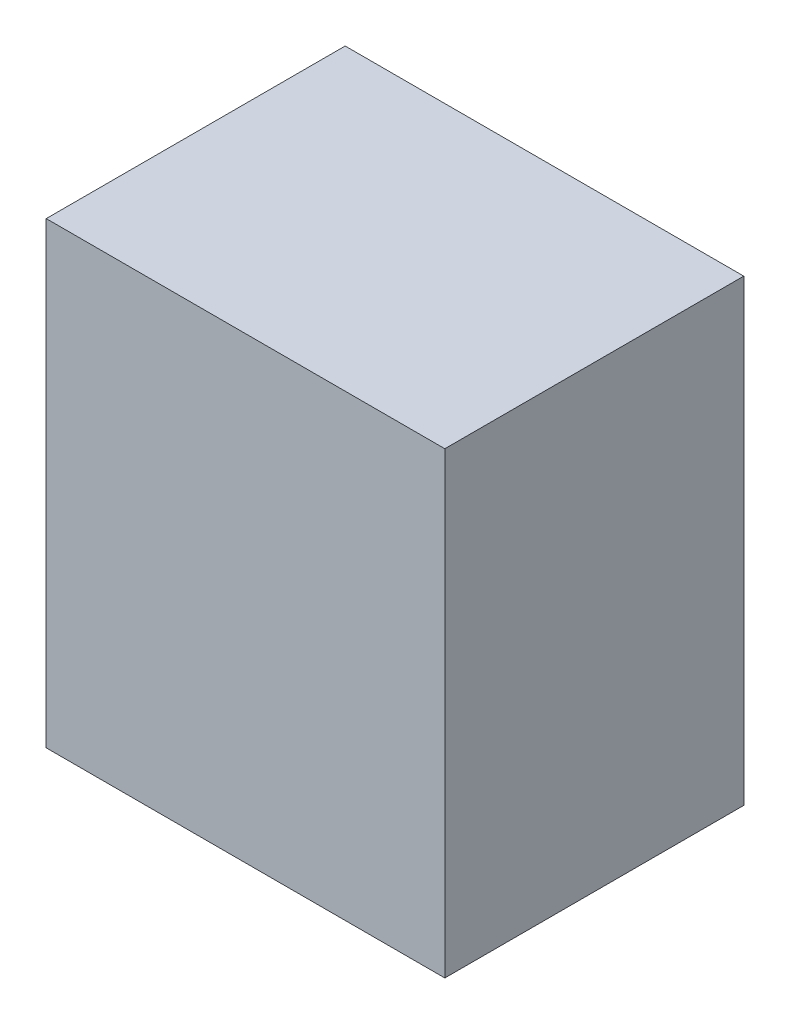
SolidWorks part; units mm, degrees
ref_plane "Front Plane" through (0, 0, 0) normal (0, 0, 1) x (1, 0, 0)
ref_plane "Top Plane" through (0, 0, 0) normal (0, 1, 0) x (1, 0, 0)
ref_plane "Right Plane" through (0, 0, 0) normal (1, 0, 0) x (0, 0, -1)
sketch "Sketch2" plane through (0, 0, 0) normal (0, 1, 0) x (1, 0, 0)
  line L1 (-10, 7.5) -> (10, 7.5)
  line L2 (-10, 7.5) -> (-10, -7.5)
  line L3 (-10, -7.5) -> (10, -7.5)
  line L4 (10, 7.5) -> (10, -7.5)
  line L5 (-10, 7.5) -> (10, -7.5) construction
  line L6 (-10, -7.5) -> (10, 7.5) construction
  point P0 (0, 0)
extrude "Boss-Extrude1" add sketch "Sketch2" along normal blind 23
